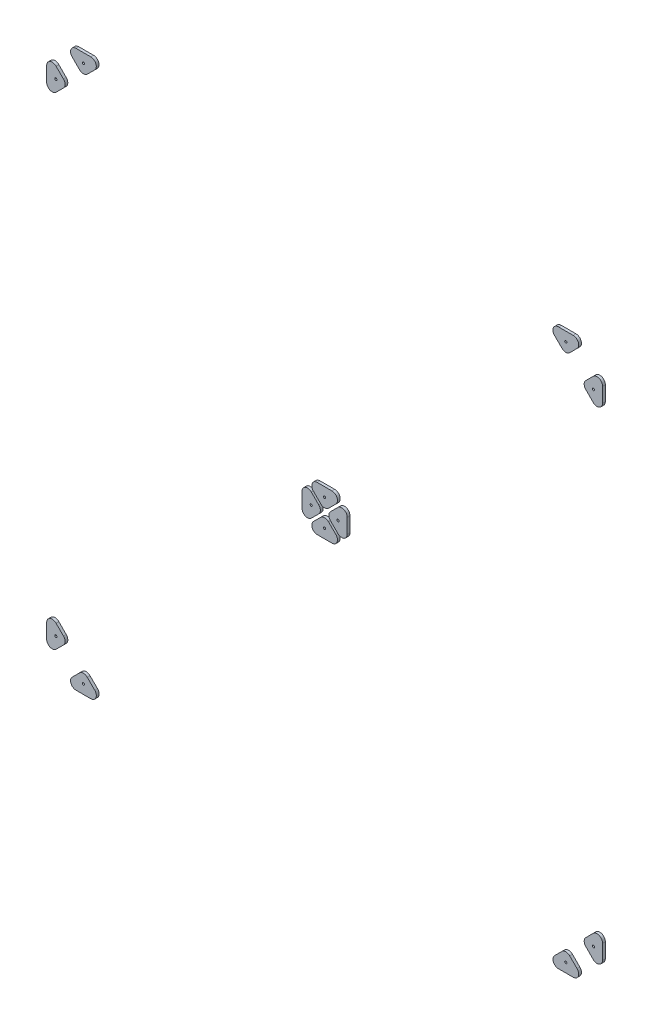
SolidWorks part; units mm, degrees
material "Plain Carbon Steel"
ref_plane "Front Plane" through (0, 0, 0) normal (0, 0, 1) x (1, 0, 0)
ref_plane "Top Plane" through (0, 0, 0) normal (0, 1, 0) x (1, 0, 0)
ref_plane "Right Plane" through (0, 0, 0) normal (1, 0, 0) x (0, 0, -1)
sketch "Sketch1" plane through (0, 0, 0) normal (0, 0, 1) x (1, 0, 0)
  line L0 (549.5147, -584.5147) -> (533.4853, -568.4853)
  line L1 (-600, -605) -> (600, -605) construction
  line L2 (516.5147, -568.4853) -> (500.4853, -584.5147)
  line L3 (508.9706, -605) -> (541.0294, -605)
  line L4 (600.7574, -605) -> (19.0919, -23.3345) construction
  line L5 (449.2426, -605) -> (525, -529.2426) construction
  line L6 (0, 0) -> (0, -665) construction
  line L7 (660, -665) -> (-660, -665) construction
  line L8 (0, 0) -> (602.8787, -602.8787) construction
  line L9 (600.7574, -605) -> (605, -600.7574) construction
  line L10 (605, -508.9706) -> (605, -541.0294)
  line L11 (568.4853, -516.5147) -> (584.5147, -500.4853)
  line L12 (584.5147, -549.5147) -> (568.4853, -533.4853)
  line L13 (-584.5147, -549.5147) -> (-568.4853, -533.4853)
  line L14 (-568.4853, -516.5147) -> (-584.5147, -500.4853)
  line L15 (-605, -508.9706) -> (-605, -541.0294)
  line L16 (-508.9706, -605) -> (-541.0294, -605)
  line L17 (-516.5147, -568.4853) -> (-500.4853, -584.5147)
  line L18 (-549.5147, -584.5147) -> (-533.4853, -568.4853)
  line L19 (0, 0) -> (-711, 0) construction
  line L20 (-711, -420) -> (-711, 420) construction
  line L21 (-549.5147, 584.5147) -> (-533.4853, 568.4853)
  line L22 (-516.5147, 568.4853) -> (-500.4853, 584.5147)
  line L23 (-508.9706, 605) -> (-541.0294, 605)
  line L24 (-605, 508.9706) -> (-605, 541.0294)
  line L25 (-568.4853, 516.5147) -> (-584.5147, 500.4853)
  line L26 (-584.5147, 549.5147) -> (-568.4853, 533.4853)
  line L27 (584.5147, 549.5147) -> (568.4853, 533.4853)
  line L28 (568.4853, 516.5147) -> (584.5147, 500.4853)
  line L29 (605, 508.9706) -> (605, 541.0294)
  line L30 (508.9706, 605) -> (541.0294, 605)
  line L31 (516.5147, 568.4853) -> (500.4853, 584.5147)
  line L32 (549.5147, 584.5147) -> (533.4853, 568.4853)
  line L33 (525, -605) -> (525, -564.9706) construction
  line L34 (0, -49.2426) -> (0, -4.2426) construction
  line L35 (16.0294, -49.2426) -> (-16.0294, -49.2426)
  line L36 (600.7574, -605) -> (19.0919, -23.3345) construction
  line L37 (-19.0919, -23.3345) -> (-600.7574, -605) construction
  line L38 (-24.5147, -28.7574) -> (-8.4853, -12.7279)
  line L39 (8.4853, -12.7279) -> (24.5147, -28.7574)
  line L40 (49.2426, 0) -> (4.2426, 0) construction
  line L41 (12.7279, -8.4853) -> (28.7574, -24.5147)
  line L42 (28.7574, 24.5147) -> (12.7279, 8.4853)
  line L43 (49.2426, -16.0294) -> (49.2426, 16.0294)
  line L44 (0, 0) -> (663.5355, 663.5355) construction
  line L45 (0, 49.2426) -> (0, 4.2426) construction
  line L46 (-49.2426, 0) -> (-4.2426, 0) construction
  line L47 (-16.0294, 49.2426) -> (16.0294, 49.2426)
  line L48 (24.5147, 28.7574) -> (8.4853, 12.7279)
  line L49 (-8.4853, 12.7279) -> (-24.5147, 28.7574)
  line L50 (-12.7279, 8.4853) -> (-28.7574, 24.5147)
  line L51 (-28.7574, -24.5147) -> (-12.7279, -8.4853)
  line L52 (-49.2426, 16.0294) -> (-49.2426, -16.0294)
  line L53 (541.5, -576.5) -> (556.8787, -561.1213) construction
  line L54 (508.5, -576.5) -> (493.1213, -561.1213) construction
  line L55 (525, -564.9706) -> (525, -560) construction
  line L56 (525, -560) -> (516.5147, -568.4853) construction
  line L57 (525, -560) -> (525, -605) construction
  circle A0 centre (525, -585) radius 2.4
  arc A1 (500.4853, -584.5147) -> (508.9706, -605) centre (508.9706, -593) ccw
  arc A2 (533.4853, -568.4853) -> (516.5147, -568.4853) centre (525, -576.9706) ccw
  arc A3 (549.5147, -584.5147) -> (541.0294, -605) centre (541.0294, -593) cw
  arc A4 (584.5147, -549.5147) -> (605, -541.0294) centre (593, -541.0294) ccw
  arc A5 (568.4853, -533.4853) -> (568.4853, -516.5147) centre (576.9706, -525) cw
  arc A6 (584.5147, -500.4853) -> (605, -508.9706) centre (593, -508.9706) cw
  circle A7 centre (585, -525) radius 2.4
  circle A8 centre (-585, -525) radius 2.4
  arc A9 (-584.5147, -500.4853) -> (-605, -508.9706) centre (-593, -508.9706) ccw
  arc A10 (-568.4853, -533.4853) -> (-568.4853, -516.5147) centre (-576.9706, -525) ccw
  arc A11 (-584.5147, -549.5147) -> (-605, -541.0294) centre (-593, -541.0294) cw
  arc A12 (-549.5147, -584.5147) -> (-541.0294, -605) centre (-541.0294, -593) ccw
  arc A13 (-533.4853, -568.4853) -> (-516.5147, -568.4853) centre (-525, -576.9706) cw
  arc A14 (-500.4853, -584.5147) -> (-508.9706, -605) centre (-508.9706, -593) cw
  circle A15 centre (-525, -585) radius 2.4
  circle A16 centre (-525, 585) radius 2.4
  arc A17 (-500.4853, 584.5147) -> (-508.9706, 605) centre (-508.9706, 593) ccw
  arc A18 (-533.4853, 568.4853) -> (-516.5147, 568.4853) centre (-525, 576.9706) ccw
  arc A19 (-549.5147, 584.5147) -> (-541.0294, 605) centre (-541.0294, 593) cw
  arc A20 (-584.5147, 549.5147) -> (-605, 541.0294) centre (-593, 541.0294) ccw
  arc A21 (-568.4853, 533.4853) -> (-568.4853, 516.5147) centre (-576.9706, 525) cw
  arc A22 (-584.5147, 500.4853) -> (-605, 508.9706) centre (-593, 508.9706) cw
  circle A23 centre (-585, 525) radius 2.4
  circle A24 centre (585, 525) radius 2.4
  arc A25 (584.5147, 500.4853) -> (605, 508.9706) centre (593, 508.9706) ccw
  arc A26 (568.4853, 533.4853) -> (568.4853, 516.5147) centre (576.9706, 525) ccw
  arc A27 (584.5147, 549.5147) -> (605, 541.0294) centre (593, 541.0294) cw
  arc A28 (549.5147, 584.5147) -> (541.0294, 605) centre (541.0294, 593) ccw
  arc A29 (533.4853, 568.4853) -> (516.5147, 568.4853) centre (525, 576.9706) cw
  arc A30 (500.4853, 584.5147) -> (508.9706, 605) centre (508.9706, 593) cw
  circle A31 centre (525, 585) radius 2.4
  arc A32 (8.4853, -12.7279) -> (-8.4853, -12.7279) centre (0, -21.2132) ccw
  arc A33 (-16.0294, -49.2426) -> (-24.5147, -28.7574) centre (-16.0294, -37.2426) cw
  arc A34 (16.0294, -49.2426) -> (24.5147, -28.7574) centre (16.0294, -37.2426) ccw
  circle A35 centre (0, -29.2426) radius 2.4
  circle A36 centre (29.2426, 0) radius 2.4
  arc A37 (49.2426, -16.0294) -> (28.7574, -24.5147) centre (37.2426, -16.0294) cw
  arc A38 (49.2426, 16.0294) -> (28.7574, 24.5147) centre (37.2426, 16.0294) ccw
  arc A39 (12.7279, -8.4853) -> (12.7279, 8.4853) centre (21.2132, 0) cw
  arc A40 (665, 660) -> (660, 665) centre (660, 660) ccw construction
  arc A41 (-8.4853, 12.7279) -> (8.4853, 12.7279) centre (0, 21.2132) ccw
  arc A42 (16.0294, 49.2426) -> (24.5147, 28.7574) centre (16.0294, 37.2426) cw
  arc A43 (-16.0294, 49.2426) -> (-24.5147, 28.7574) centre (-16.0294, 37.2426) ccw
  circle A44 centre (0, 29.2426) radius 2.4
  circle A45 centre (-29.2426, 0) radius 2.4
  arc A46 (-49.2426, 16.0294) -> (-28.7574, 24.5147) centre (-37.2426, 16.0294) cw
  arc A47 (-49.2426, -16.0294) -> (-28.7574, -24.5147) centre (-37.2426, -16.0294) ccw
  arc A48 (-12.7279, 8.4853) -> (-12.7279, -8.4853) centre (-21.2132, 0) cw
  point P13 (480, -605)
  point P18 (570, -605)
  point P38 (605, -570)
  point P39 (605, -480)
  point P62 (-605, -480)
  point P63 (-605, -570)
  point P64 (-570, -605)
  point P65 (-480, -605)
  point P113 (-480, 605)
  point P114 (-570, 605)
  point P115 (-605, 570)
  point P116 (-605, 480)
  point P117 (605, 480)
  point P118 (605, 570)
  point P119 (570, 605)
  point P120 (480, 605)
  point P137 (-45, -49.2426)
  point P140 (45, -49.2426)
  point P156 (49.2426, -45)
  point P157 (49.2426, 45)
  point P188 (45, 49.2426)
  point P189 (-45, 49.2426)
  point P190 (-49.2426, 45)
  point P191 (-49.2426, -45)
  dimension "D4" = 4.8
  dimension "D5" = 12
  dimension "D6" = 12
  dimension "D7" = 4.8
  dimension "D1" = 45
  dimension "D2" = 45
  dimension "D3" = 20
  dimension "D8" = 20
extrude "Boss-Extrude1" add sketch "Sketch1" against normal blind 6
